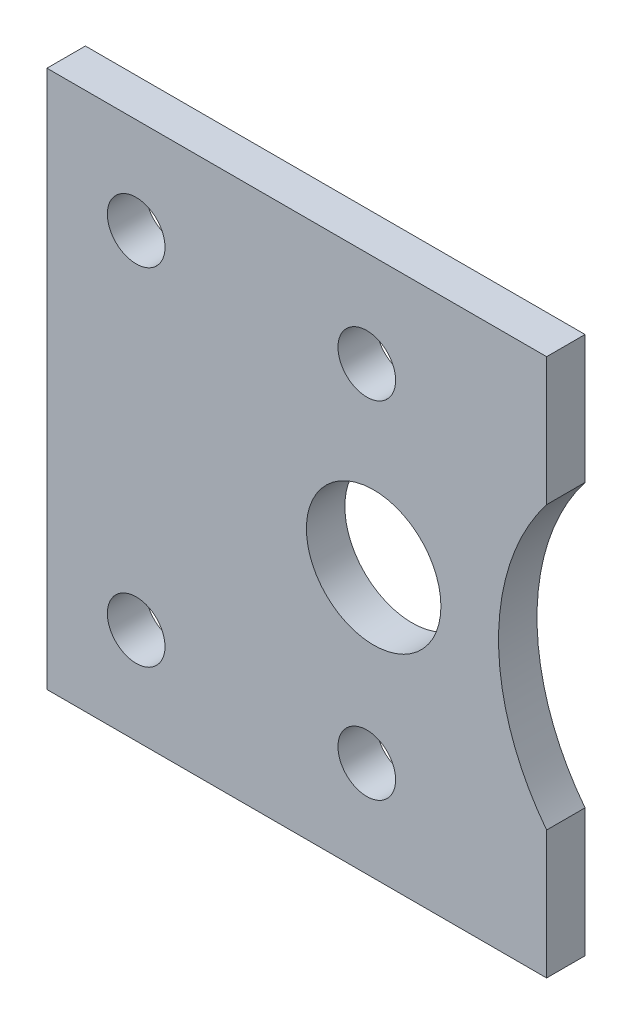
SolidWorks part; units mm, degrees
ref_plane "Front Plane" through (0, 0, 0) normal (0, 0, 1) x (1, 0, 0)
ref_plane "Top Plane" through (0, 0, 0) normal (0, 1, 0) x (1, 0, 0)
ref_plane "Right Plane" through (0, 0, 0) normal (1, 0, 0) x (0, 0, -1)
sketch "Sketch1" plane through (0, 0, 0) normal (0, 0, 1) x (1, 0, 0)
  line L0 (-13, 0) -> (10.5, 0) construction
  line L1 (-13, -14) -> (13, -14)
  line L2 (-13, -14) -> (-13, 14)
  line L3 (-13, 14) -> (13, 14)
  line L4 (13, -14) -> (13, -7.3314)
  line L5 (-13, -14) -> (13, 14) construction
  line L6 (-13, 14) -> (13, -14) construction
  line L7 (13, 7.3314) -> (13, 14)
  circle A0 centre (-8.3571, 9) radius 1.5
  circle A1 centre (4, 0) radius 3.5
  arc A2 (13, 7.3314) -> (13, -7.3314) centre (22.5, 0) ccw
  circle A3 centre (3.6429, 9) radius 1.5
  circle A4 centre (3.6429, -9) radius 1.5
  circle A5 centre (-8.3571, -9) radius 1.5
  point P0 (0, 0)
  dimension "D3" = 5
  dimension "D4" = 3
  dimension "D5" = 7
  dimension "D6" = 24
  dimension "D7" = 18.5
  dimension "D8" = 17
  dimension "D1" = 26
  dimension "D2" = 28
  dimension "D9" = 2
  dimension "D10" = 2
extrude "Boss-Extrude1" add sketch "Sketch1" along normal blind 2
